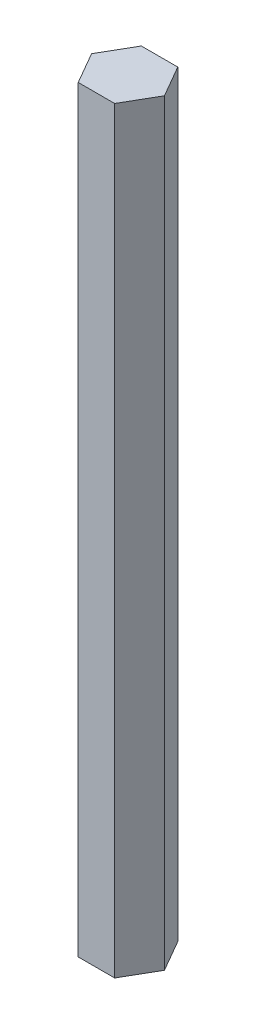
SolidWorks part; units mm, degrees
ref_plane "Front Plane" through (0, 0, 0) normal (0, 0, 1) x (1, 0, 0)
ref_plane "Top Plane" through (0, 0, 0) normal (0, 1, 0) x (1, 0, 0)
ref_plane "Right Plane" through (0, 0, 0) normal (1, 0, 0) x (0, 0, -1)
sketch "Sketch1" plane through (0, 0, 0) normal (0, 1, 0) x (1, 0, 0)
  line L1 (3.6662, -6.35) -> (7.3323, 0)
  line L2 (7.3323, 0) -> (3.6662, 6.35)
  line L3 (3.6662, 6.35) -> (-3.6662, 6.35)
  line L4 (-3.6662, 6.35) -> (-7.3323, 0)
  line L5 (-7.3323, 0) -> (-3.6662, -6.35)
  line L6 (-3.6662, -6.35) -> (3.6662, -6.35)
  circle A0 centre (0, 0) radius 6.35 construction
  point P1 (3.488, 6.4496)
  dimension "D1" = 12.7
extrude "Boss-Extrude1" add sketch "Sketch1" along normal blind 152.4
